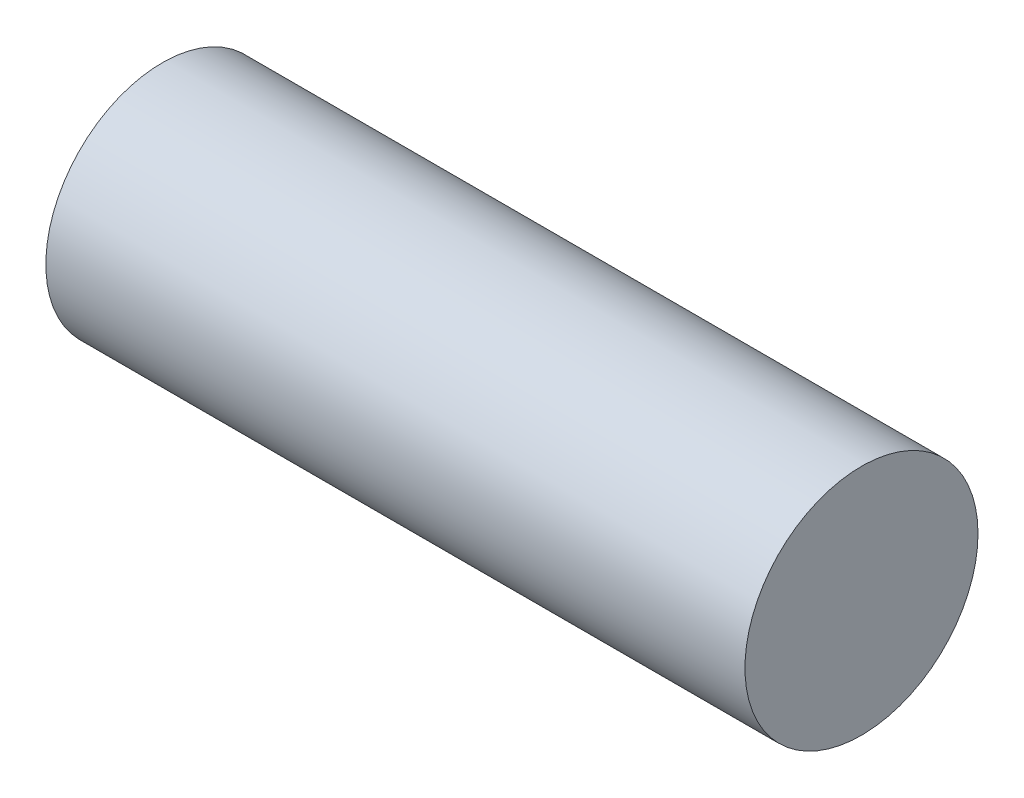
SolidWorks part; units mm, degrees
material "Brass"
ref_plane "Front Plane" through (0, 0, 0) normal (0, 0, 1) x (1, 0, 0)
ref_plane "Top Plane" through (0, 0, 0) normal (0, 1, 0) x (1, 0, 0)
ref_plane "Right Plane" through (0, 0, 0) normal (1, 0, 0) x (0, 0, -1)
sketch "Sketch1" plane through (0, 0, 0) normal (1, 0, 0) x (0, 0, -1)
  circle A0 centre (0, 0) radius 15
  dimension "D1" = 30
extrude "Boss-Extrude1" add sketch "Sketch1" along normal blind 90
